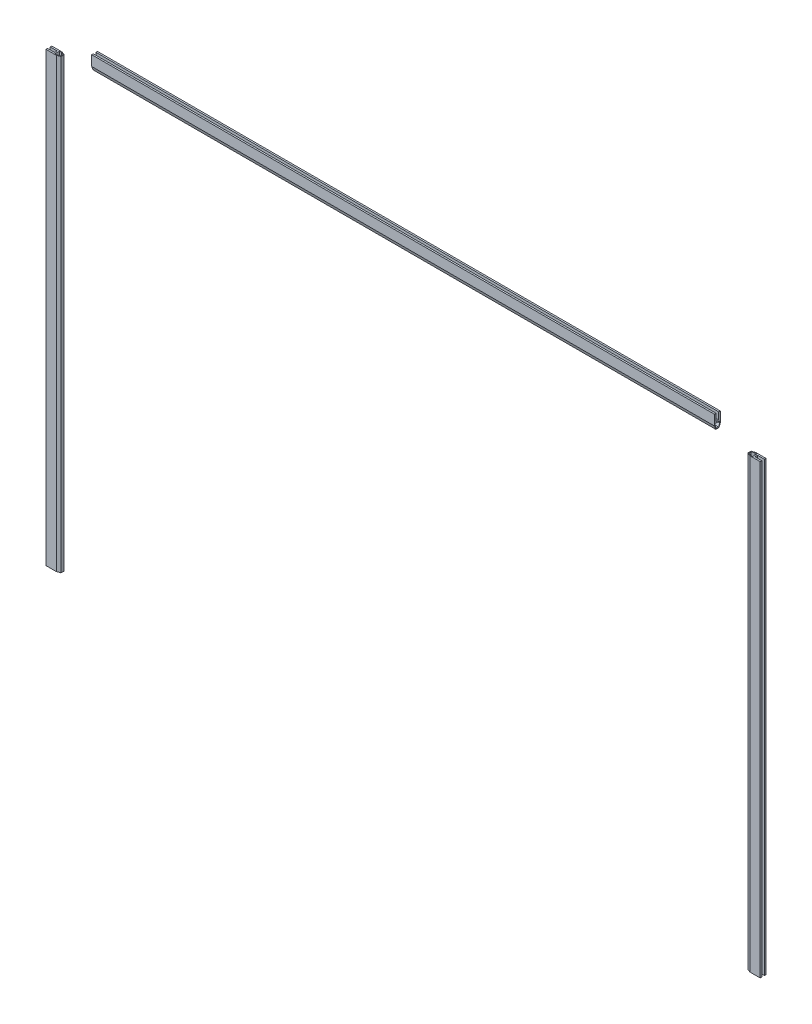
SolidWorks part; units mm, degrees
ref_plane "Plan de face" through (0, 0, 0) normal (0, 0, 1) x (1, 0, 0)
ref_plane "Plan de dessus" through (0, 0, 0) normal (0, 1, 0) x (1, 0, 0)
ref_plane "Plan de droite" through (0, 0, 0) normal (1, 0, 0) x (0, 0, -1)
sketch "Esquisse1" plane through (0, 0, 0) normal (0, 0, 1) x (1, 0, 0)
  line L0 (-548, 0) -> (548, 0) construction
  line L1 (-548, 0) -> (-548, 717.5) construction
  line L2 (-548, 0) -> (-548, 700)
  line L3 (548, 0) -> (548, 700)
  line L4 (-548, 717.5) -> (548, 717.5) construction
  line L5 (-487.5, 717.5) -> (487.5, 717.5)
  line L7 (548, 717.5) -> (548, 0) construction
  line L8 (0, 0) -> (0, 717.5) construction
  dimension "D1" = 1096
  dimension "D2" = 717.5
  dimension "D3" = 975
  dimension "D4" = 700
other "Joint 99168010 JOINT DE CARROSSERIE(1)"
ref_plane "Plan1" through (-548, 0, 0) normal (0, 1, 0) x (-1, 0, 0)
sketch "Sketch1" plane through (-548, 0, 0) normal (0, 1, 0) x (-1, 0, 0)
  line L0 (11, 4.5) -> (-5.005, 4.5)
  line L1 (-5.005, 4.5) -> (-10.5, 2.5)
  line L2 (-10.5, 2.5) -> (-10.5, -2.5)
  line L3 (-10.5, -2.5) -> (-5.005, -4.5)
  line L4 (-5.005, -4.5) -> (11, -4.5)
  line L5 (11, -4.5) -> (11, -2)
  line L6 (11, -2) -> (0, -2)
  line L7 (0, -2) -> (0, 2)
  line L8 (0, 2) -> (11, 2)
  line L9 (11, 2) -> (11, 4.5)
  line L10 (-4.8287, 3.5) -> (-9.5, 1.7998)
  line L11 (-9.5, 1.7998) -> (-9.5, -1.7998)
  line L12 (-9.5, -1.7998) -> (-4.8287, -3.5)
  line L13 (-4.8287, -3.5) -> (-2, -3.5)
  line L14 (0, 0) -> (-10.5, 0) construction
  line L15 (-2, -3.5) -> (-2, 3.5)
  line L16 (-2, 3.5) -> (-4.8287, 3.5)
  point P16 (-9.5, 0)
  point P19 (-2, 0)
  point P20 (0, 0)
  dimension "D4" = 11
  dimension "D5" = 1
  dimension "D2" = 9
  dimension "D8" = 70
  dimension "D1" = 4
  dimension "D3" = 21.5
  dimension "D6" = 1
  dimension "D7" = 5
  dimension "D9" = 1
  dimension "D10" = 2
